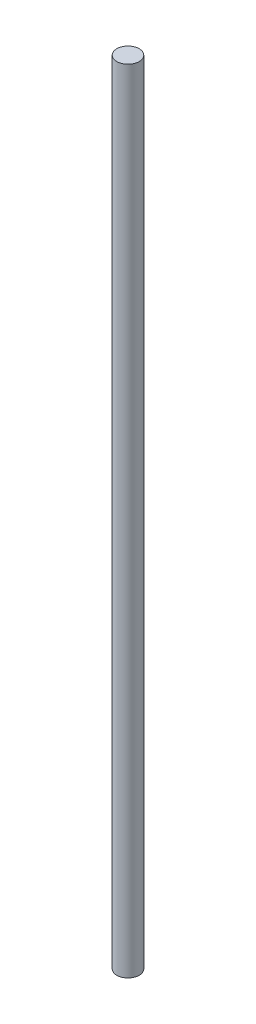
SolidWorks part; units mm, degrees
ref_plane "Front Plane" through (0, 0, 0) normal (0, 0, 1) x (1, 0, 0)
ref_plane "Top Plane" through (0, 0, 0) normal (0, 1, 0) x (1, 0, 0)
ref_plane "Right Plane" through (0, 0, 0) normal (1, 0, 0) x (0, 0, -1)
sketch "Sketch1" plane through (0, 0, 0) normal (0, 1, 0) x (1, 0, 0)
  circle A0 centre (0, 0) radius 6.35
  dimension "D1" = 12.7
extrude "Boss-Extrude1" add sketch "Sketch1" along normal blind 450
equation "\"m3 hole\"= 3.2"
equation "\"m4 hole\"= 4.2"
equation "\"m5 hole\"= 5.2"
equation "\"m6 hole\"= 6.2"
equation "\"m8 hole\"= 8.2"
equation "\"m3 tapped\"= 2.5"
equation "\"m4 tapped\"= 3.3"
equation "\"m5 tapped\"= 4.2"
equation "\"m6 tapped\"= 5"
equation "\"m8 tapped\"= 6.8"
